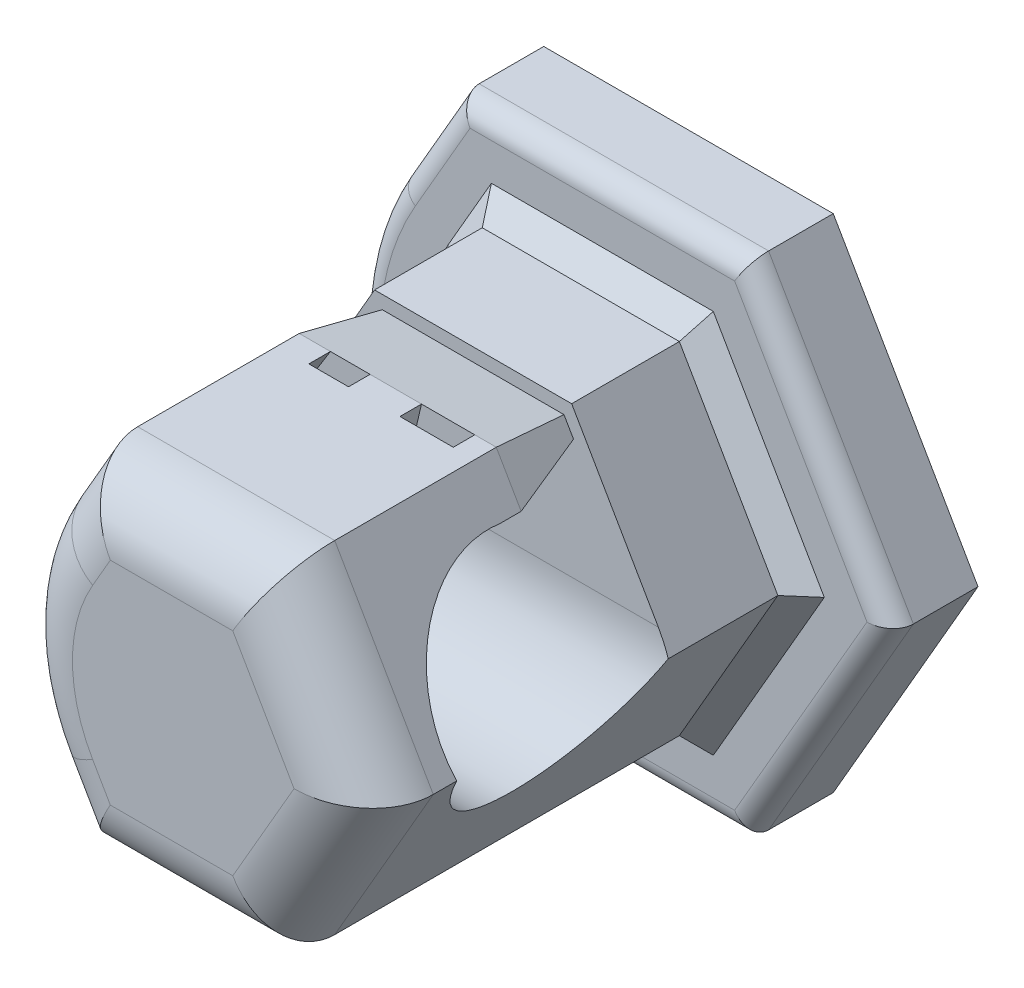
SolidWorks part; units mm, degrees
material "ABS"
ref_plane "Front Plane" through (0, 0, 0) normal (0, 0, 1) x (1, 0, 0)
ref_plane "Top Plane" through (0, 0, 0) normal (0, 1, 0) x (1, 0, 0)
ref_plane "Right Plane" through (0, 0, 0) normal (1, 0, 0) x (0, 0, -1)
sketch "Sketch1" plane through (0, 0, 0) normal (0, 0, 1) x (1, 0, 0)
  line L0 (-19.9357, -2.6852) -> (-18.4517, -5.2555) construction
  line L1 (-18.4517, -5.2555) -> (-11.4423, -5.2555) construction
  line L2 (-11.4423, -5.2555) -> (-7.9376, 0.8148) construction
  line L3 (-7.9376, 0.8148) -> (-11.4423, 6.8852) construction
  line L4 (-11.4423, 6.8852) -> (-18.4517, 6.8852) construction
  line L5 (-18.4517, 6.8852) -> (-19.9357, 4.3148) construction
  line L6 (-18.3073, 6.6352) -> (-19.7192, 4.1898)
  line L7 (-19.7192, -2.5602) -> (-18.3073, -5.0055)
  line L8 (-18.3073, -5.0055) -> (-11.5866, -5.0055)
  line L9 (-11.5866, -5.0055) -> (-8.2263, 0.8148)
  line L10 (-8.2263, 0.8148) -> (-11.5866, 6.6352)
  line L11 (-11.5866, 6.6352) -> (-18.3073, 6.6352)
  arc A0 (-19.9357, 4.3148) -> (-19.9357, -2.6852) centre (-13.8735, 0.8148) ccw construction
  arc A1 (-19.7192, 4.1898) -> (-19.7192, -2.5602) centre (-13.8735, 0.8148) ccw
  dimension "D1" = 0.25
extrude "Boss-Extrude1" add sketch "Sketch1" along normal blind 2
sketch "Sketch2" plane through (0, 0, 2) normal (0, 0, 1) x (1, 0, 0)
  line L0 (-18.3073, -5.0055) -> (-11.5866, 6.6352) construction
  line L2 (-10.372, 0.8148) -> (-12.6595, 4.7769)
  line L3 (-12.6595, 4.7769) -> (-17.2345, 4.7769)
  line L4 (-17.2345, 4.7769) -> (-19.522, 0.8148)
  line L5 (-19.522, 0.8148) -> (-17.2345, -3.1472)
  line L6 (-17.2345, -3.1472) -> (-12.6595, -3.1472)
  line L7 (-12.6595, -3.1472) -> (-10.372, 0.8148)
  circle A0 centre (-14.947, 0.8148) radius 3.9621 construction
  dimension "D1" = 9.15
extrude "Boss-Extrude2" add sketch "Sketch2" along normal blind 10
fillet "Fillet1" radius 5 1 edges at (-19.522, 0.8148, 7)
fillet "Fillet3" radius 1.5 7 edges at (-14.947, 4.7769, 12) (-11.5157, 2.7959, 12) (-11.5157, -1.1662, 12) (-14.947, -3.1472, 12) (-17.6565, -2.4162, 12) (-18.7485, 0.8148, 12) (-17.6565, 4.0459, 12)
chamfer "Chamfer2" distance 0.5 angle 45 7 edges at (-17.6565, -2.4162, 2) (-18.7485, 0.8148, 2) (-14.947, -3.1472, 2) (-11.5157, -1.1662, 2) (-17.6565, 4.0459, 2) (-14.947, 4.7769, 2) (-11.5157, 2.7959, 2)
sketch "Sketch5" plane through (0, 0, 0) normal (0, 0, -1) x (-1, 0, 0)
  line L0 (11.0494, -4.075) -> (18.5267, -4.075) construction
  line L1 (11.5866, -5.0055) -> (8.2263, 0.8148) construction
  arc A0 (19.7192, -2.5602) -> (19.7192, 4.1898) centre (13.8735, 0.8148) ccw construction
  text T0 "3" font "Verdana" height 9
extrude "Cut-Extrude3" cut sketch "Sketch5" against normal blind 0.5
sketch "Sketch6" plane through (0, 0, 0) normal (1, 0, 0) x (0, 0, -1)
  line L0 (-10.5, 4.7769) -> (-2.5, 4.7769) construction
  line L1 (-5, 1.2894) -> (-10, 1.2894) construction
  line L2 (-5, 4.7769) -> (-5, 1.2894)
  line L5 (-7.25, 4.7769) -> (-7.25, 3.7769)
  line L6 (-7.25, 4.7769) -> (-5, 4.7769)
  arc A1 (-5, 1.2894) -> (-7.25, 3.7769) centre (-7.5, 1.2894) cw
  dimension "D1" = 1
  dimension "D4" = 2.5
  dimension "D2" = 7.5
  dimension "D3" = 2.25
extrude "Cut-Extrude4" cut sketch "Sketch6" against normal through all
sketch "Sketch7" plane through (0, 0, 7.25) normal (0, 0, -1) x (-1, 0, 0)
  line L0 (13.1578, 4.7769) -> (13.2454, 3.7769)
  line L1 (14.3953, 4.7769) -> (14.6273, 3.7769)
  line L2 (15.5894, 4.7769) -> (16.0009, 3.7769)
  line L3 (16.5096, 4.7769) -> (17.1284, 3.7769)
  line L4 (12.0821, 3.7769) -> (17.8118, 3.7769)
  line L5 (17.8118, 3.7769) -> (17.2345, 4.7769)
  line L6 (17.2345, 4.7769) -> (12.6595, 4.7769)
  line L7 (12.6595, 4.7769) -> (12.0821, 3.7769)
  line L8 (12.0821, 3.7769) -> (17.8118, 3.7769)
  line L9 (17.8118, 3.7769) -> (17.2345, 4.7769)
  line L10 (17.2345, 4.7769) -> (12.6595, 4.7769)
  line L11 (12.6595, 4.7769) -> (12.0821, 3.7769)
  line M5 (12.0821, 3.7769) -> (17.8118, 3.7769)
  line M6 (17.8118, 3.7769) -> (17.2345, 4.7769)
  line M7 (17.2345, 4.7769) -> (12.6595, 4.7769)
  line M8 (12.6595, 4.7769) -> (12.0821, 3.7769)
  dimension "D1" = 0
extrude "Boss-Extrude3" add sketch "Sketch7" along normal blind 0.5 contours L0 M7 M8 M5 | L2 L1 M7 M5 | L3 M7 M5 M6
sketch "Sketch8" plane through (0, 0, 6.75) normal (0, 0, -1) x (-1, 0, 0)
  line L0 (17.2345, 4.7769) -> (16.5096, 4.7769) construction
  line L1 (16.5096, 4.7769) -> (17.1284, 3.7769) construction
  line L2 (17.1284, 3.7769) -> (17.8118, 3.7769) construction
  line L3 (17.8118, 3.7769) -> (17.2345, 4.7769) construction
  line L4 (17.1284, 3.7769) -> (16.5096, 4.7769) construction
  line L5 (16.5096, 4.7769) -> (15.5894, 4.7769) construction
  line L6 (15.5894, 4.7769) -> (16.0009, 3.7769) construction
  line L7 (16.0009, 3.7769) -> (17.1284, 3.7769) construction
  line L8 (16.0009, 3.7769) -> (15.5894, 4.7769) construction
  line L9 (15.5894, 4.7769) -> (14.3953, 4.7769) construction
  line L10 (14.3953, 4.7769) -> (14.6273, 3.7769) construction
  line L11 (14.6273, 3.7769) -> (16.0009, 3.7769) construction
  line L12 (14.6273, 3.7769) -> (14.3953, 4.7769) construction
  line L13 (14.3953, 4.7769) -> (13.1578, 4.7769) construction
  line L14 (13.1578, 4.7769) -> (13.2454, 3.7769) construction
  line L15 (13.2454, 3.7769) -> (14.6273, 3.7769) construction
  line L16 (13.2454, 3.7769) -> (13.1578, 4.7769) construction
  line L17 (13.1578, 4.7769) -> (12.6595, 4.7769) construction
  line L18 (12.6595, 4.7769) -> (12.0821, 3.7769) construction
  line L19 (12.0821, 3.7769) -> (13.2454, 3.7769) construction
  line L20 (17.2345, 4.7769) -> (16.5096, 4.7769)
  line L21 (16.5096, 4.7769) -> (17.1284, 3.7769)
  line L22 (17.1284, 3.7769) -> (17.8118, 3.7769)
  line L23 (17.8118, 3.7769) -> (17.2345, 4.7769)
  line L24 (17.1284, 3.7769) -> (16.5096, 4.7769)
  line L25 (16.5096, 4.7769) -> (15.5894, 4.7769)
  line L26 (15.5894, 4.7769) -> (16.0009, 3.7769)
  line L27 (16.0009, 3.7769) -> (17.1284, 3.7769)
  line L28 (16.0009, 3.7769) -> (15.5894, 4.7769)
  line L29 (15.5894, 4.7769) -> (14.3953, 4.7769)
  line L30 (14.3953, 4.7769) -> (14.6273, 3.7769)
  line L31 (14.6273, 3.7769) -> (16.0009, 3.7769)
  line L32 (14.6273, 3.7769) -> (14.3953, 4.7769)
  line L33 (14.3953, 4.7769) -> (13.1578, 4.7769)
  line L34 (13.1578, 4.7769) -> (13.2454, 3.7769)
  line L35 (13.2454, 3.7769) -> (14.6273, 3.7769)
  line L36 (13.2454, 3.7769) -> (13.1578, 4.7769)
  line L37 (13.1578, 4.7769) -> (12.6595, 4.7769)
  line L38 (12.6595, 4.7769) -> (12.0821, 3.7769)
  line L39 (12.0821, 3.7769) -> (13.2454, 3.7769)
  line M1 (13.2454, 3.7769) -> (13.1578, 4.7769)
  line M2 (13.1578, 4.7769) -> (12.6595, 4.7769)
  line M3 (12.6595, 4.7769) -> (12.0821, 3.7769)
  line M4 (12.0821, 3.7769) -> (13.2454, 3.7769)
extrude "Boss-Extrude4" add sketch "Sketch8" along normal up to surface (1.75 mm away) draft 10 contours M4 M1 M2 M3 | L35 L30 L33 M1 | L30 L31 L26 L29 | L26 L27 L21 L25 | L22 L23 L20 L21
fillet "Fillet4" radius 0.5 7 edges at (-19.0132, 5.4125, 2) (-14.947, 6.6352, 2) (-9.9064, 3.725, 2) (-9.9064, -2.0953, 2) (-14.947, -5.0055, 2) (-19.0132, -3.7828, 2) (-20.6235, 0.8148, 2)
